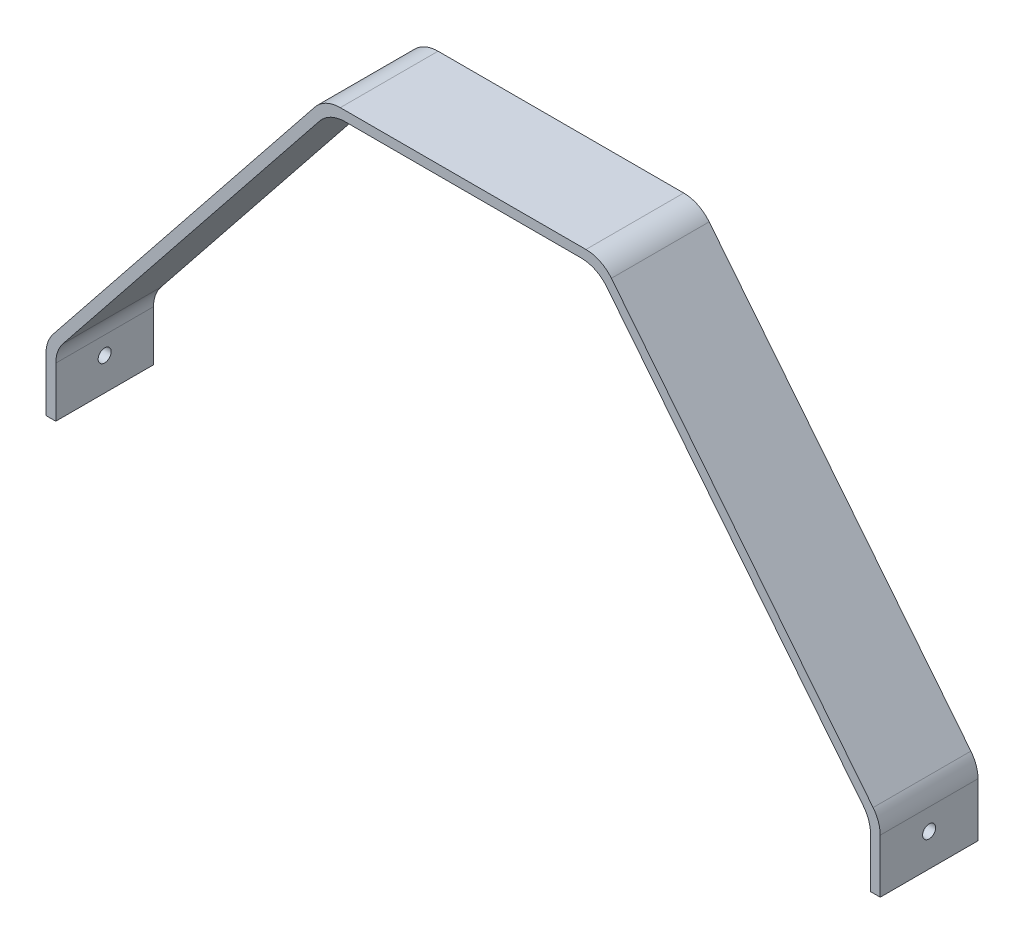
SolidWorks part; units mm, degrees
ref_plane "Front Plane" through (0, 0, 0) normal (0, 0, 1) x (1, 0, 0)
ref_plane "Top Plane" through (0, 0, 0) normal (0, 1, 0) x (1, 0, 0)
ref_plane "Right Plane" through (0, 0, 0) normal (1, 0, 0) x (0, 0, -1)
sketch "Sketch1" plane through (0, 0, 0) normal (0, 0, 1) x (1, 0, 0)
  line L0 (-42.5, 0) -> (42.5, 0)
  line L5 (0, 0) -> (0, -127) construction
  line L6 (42.5, 0) -> (128, -107)
  line L7 (-128, -127) -> (128, -127) construction
  line L8 (128, -127) -> (128, -107)
  line L9 (-128, -127) -> (-128, -107)
  line L10 (-42.5, 0) -> (-128, -107)
  line L11 (-125, -127) -> (-125, -108.0514)
  line L12 (-41.0571, -3) -> (-125, -108.0514)
  line L13 (-41.0571, -3) -> (41.0571, -3)
  line L14 (41.0571, -3) -> (125, -108.0514)
  line L15 (125, -127) -> (125, -108.0514)
  line L16 (-128, -127) -> (-125, -127)
  line L17 (128, -127) -> (125, -127)
  line L18 (125, -127) -> (128, -127)
  line L19 (-128, -127) -> (-125, -127)
  point P3 (0, 0)
  point P13 (0, -127)
  dimension "D1" = 85
  dimension "D2" = 127
  dimension "D3" = 256
  dimension "D4" = 20
  dimension "D5" = 3
extrude "Boss-Extrude1" add sketch "Sketch1" along normal blind 30 contours L17 L8 L6 L0 L10 L9 L16 L11 L12 L13 L14 L15
sketch "Sketch2" plane through (128, 0, 0) normal (1, 0, 0) x (0, 0, -1)
  line L0 (-30, -107) -> (0, -127) construction
  circle A0 centre (-15, -117) radius 2
  dimension "D1" = 4
fillet "Fillet1" radius 10 8 edges at (-125, -108.0514, 15) (-41.0571, -3, 15) (125, -108.0514, 15) (41.0571, -3, 15) (-128, -107, 15) (-42.5, 0, 15) (42.5, 0, 15) (128, -107, 15)
extrude "Cut-Extrude1" cut sketch "Sketch2" against normal through all both
